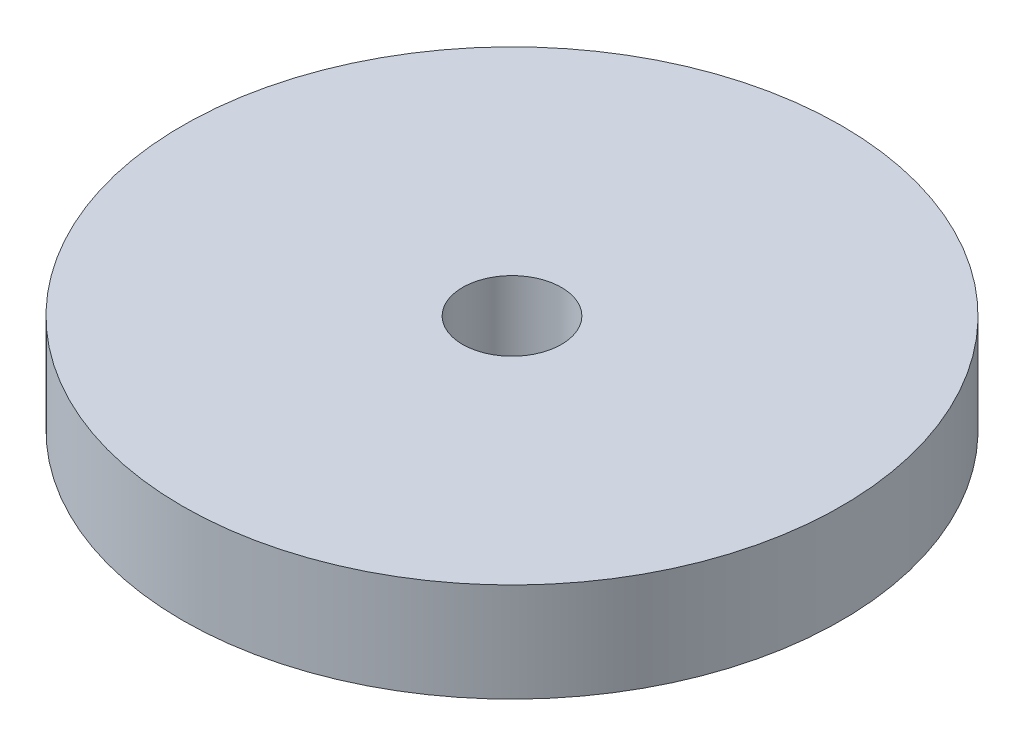
SolidWorks part; units mm, degrees
ref_plane "Front Plane" through (0, 0, 0) normal (0, 0, 1) x (1, 0, 0)
ref_plane "Top Plane" through (0, 0, 0) normal (0, 1, 0) x (1, 0, 0)
ref_plane "Right Plane" through (0, 0, 0) normal (1, 0, 0) x (0, 0, -1)
sketch "Sketch1" plane through (0, 0, 0) normal (0, 1, 0) x (1, 0, 0)
  circle A0 centre (0, 0) radius 10
  circle A1 centre (0, 0) radius 1.5
  dimension "D1" = 20
  dimension "D2" = 3
extrude "Boss-Extrude1" add sketch "Sketch1" along normal blind 3
